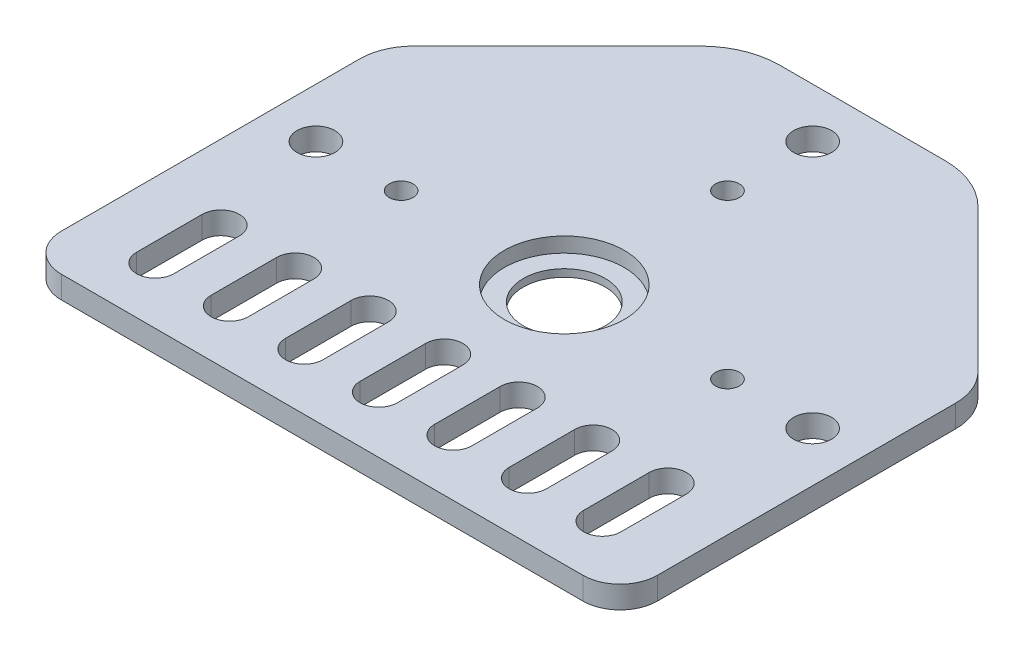
SolidWorks part; units mm, degrees
ref_plane "Front" through (0, 0, 0) normal (0, 0, 1) x (1, 0, 0)
ref_plane "Top" through (0, 0, 0) normal (0, 1, 0) x (1, 0, 0)
ref_plane "Right" through (0, 0, 0) normal (1, 0, 0) x (0, 0, -1)
sketch "Sketch1" plane through (0, 0, 0) normal (0, 1, 0) x (1, 0, 0)
  line L0 (-37.8619, 50.1619) -> (-18.6577, 69.366)
  line L1 (-35, 0) -> (35, 0)
  line L2 (-40, 5) -> (-40, 45)
  line L3 (-11.0917, 72.5) -> (11.0917, 72.5)
  line L4 (40, 5) -> (40, 45)
  line L5 (18.6577, 69.366) -> (37.8619, 50.1619)
  line L6 (0, 0) -> (0, 72.5) construction
  line L7 (0, 32.5) -> (-40, 32.5) construction
  line L8 (0, 7.6) -> (0, 16.4) construction
  line L9 (-2.5, 7.6) -> (-2.5, 16.4)
  line L10 (2.5, 7.6) -> (2.5, 16.4)
  line L11 (10, 7.6) -> (10, 16.4) construction
  line L12 (7.5, 7.6) -> (7.5, 16.4)
  line L13 (12.5, 7.6) -> (12.5, 16.4)
  line L14 (20, 7.6) -> (20, 16.4) construction
  line L15 (17.5, 7.6) -> (17.5, 16.4)
  line L16 (22.5, 7.6) -> (22.5, 16.4)
  line L17 (30, 7.6) -> (30, 16.4) construction
  line L18 (27.5, 7.6) -> (27.5, 16.4)
  line L19 (32.5, 7.6) -> (32.5, 16.4)
  line L20 (-10, 7.6) -> (-10, 16.4) construction
  line L21 (-7.5, 7.6) -> (-7.5, 16.4)
  line L22 (-12.5, 7.6) -> (-12.5, 16.4)
  line L23 (-20, 7.6) -> (-20, 16.4) construction
  line L24 (-17.5, 7.6) -> (-17.5, 16.4)
  line L25 (-22.5, 7.6) -> (-22.5, 16.4)
  line L26 (-30, 7.6) -> (-30, 16.4) construction
  line L27 (-27.5, 7.6) -> (-27.5, 16.4)
  line L28 (-32.5, 7.6) -> (-32.5, 16.4)
  arc A0 (-11.0917, 72.5) -> (-18.6577, 69.366) centre (-11.0917, 61.8) ccw
  arc A1 (18.6577, 69.366) -> (11.0917, 72.5) centre (11.0917, 61.8) ccw
  arc A2 (-37.8619, 50.1619) -> (-40, 45) centre (-32.7, 45) ccw
  arc A3 (40, 45) -> (37.8619, 50.1619) centre (32.7, 45) ccw
  arc A4 (-40, 5) -> (-35, 0) centre (-35, 5) ccw
  arc A5 (35, 0) -> (40, 5) centre (35, 5) ccw
  circle A6 centre (0, 32.5) radius 5.5
  circle A7 centre (0, 65.83) radius 2.55
  circle A8 centre (0, 54.4) radius 1.6
  circle A9 centre (-33.33, 32.5) radius 2.55
  circle A10 centre (-21.9, 32.5) radius 1.6
  circle A11 centre (33.33, 32.5) radius 2.55
  circle A12 centre (21.9, 32.5) radius 1.6
  arc A13 (-2.5, 7.6) -> (2.5, 7.6) centre (0, 7.6) ccw
  arc A14 (2.5, 16.4) -> (-2.5, 16.4) centre (0, 16.4) ccw
  arc A15 (7.5, 7.6) -> (12.5, 7.6) centre (10, 7.6) ccw
  arc A16 (12.5, 16.4) -> (7.5, 16.4) centre (10, 16.4) ccw
  arc A17 (17.5, 7.6) -> (22.5, 7.6) centre (20, 7.6) ccw
  arc A18 (22.5, 16.4) -> (17.5, 16.4) centre (20, 16.4) ccw
  arc A19 (27.5, 7.6) -> (32.5, 7.6) centre (30, 7.6) ccw
  arc A20 (32.5, 16.4) -> (27.5, 16.4) centre (30, 16.4) ccw
  arc A21 (-7.5, 7.6) -> (-12.5, 7.6) centre (-10, 7.6) cw
  arc A22 (-12.5, 16.4) -> (-7.5, 16.4) centre (-10, 16.4) cw
  arc A23 (-17.5, 7.6) -> (-22.5, 7.6) centre (-20, 7.6) cw
  arc A24 (-22.5, 16.4) -> (-17.5, 16.4) centre (-20, 16.4) cw
  arc A25 (-27.5, 7.6) -> (-32.5, 7.6) centre (-30, 7.6) cw
  arc A26 (-32.5, 16.4) -> (-27.5, 16.4) centre (-30, 16.4) cw
  point P38 (0, 12)
  point P47 (10, 12)
  point P54 (20, 12)
  point P61 (30, 12)
  point P67 (-10, 12)
  point P74 (-20, 12)
  point P81 (-30, 12)
  dimension "D1" = 10.7
  dimension "D2" = 7.3
  dimension "D3" = 5
  dimension "D7" = 11
  dimension "D6" = 5.1
  dimension "D10" = 11.43
  dimension "D11" = 5
  dimension "D12" = 13.8
  dimension "D16" = 3.2
  dimension "D4" = 40
  dimension "D5" = 72.5
  dimension "D8" = 80
  dimension "D9" = 33.33
  dimension "D13" = 18.9
  dimension "D15" = 10
  dimension "D17" = 21.9
  dimension "D18" = 21.9
  dimension "D19" = 135
  dimension "D20" = 27.1588
  dimension "D14" = 4
extrude "Boss-Extrude1" add sketch "Sketch1" along normal blind 3
sketch "Sketch2" plane through (0, 3, 0) normal (0, 1, 0) x (1, 0, 0)
  circle A0 centre (0, 32.5) radius 8.05
  dimension "D1" = 16.1
extrude "Cut-Extrude1" cut sketch "Sketch2" against normal blind 2
